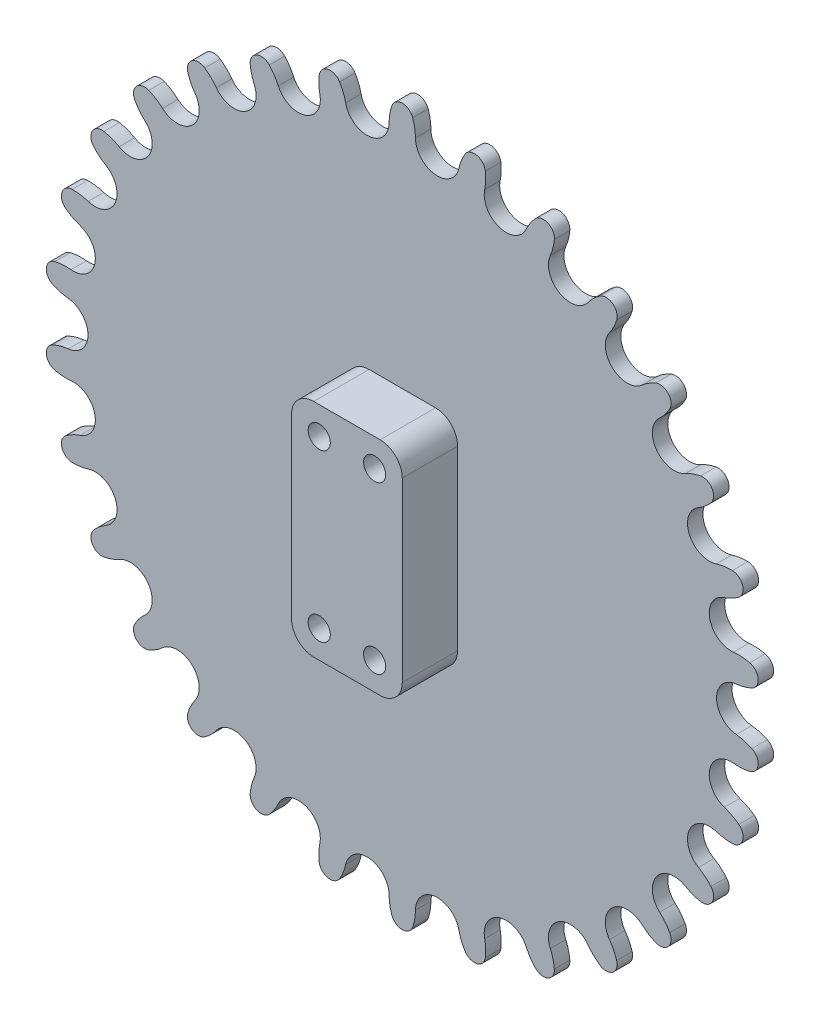
SolidWorks part; units mm, degrees
ref_plane "Front Plane" through (0, 0, 0) normal (0, 0, 1) x (1, 0, 0)
ref_plane "Top Plane" through (0, 0, 0) normal (0, 1, 0) x (1, 0, 0)
ref_plane "Right Plane" through (0, 0, 0) normal (1, 0, 0) x (0, 0, -1)
sketch "Sketch2" plane through (0, 0, 0) normal (0, 0, 1) x (1, 0, 0)
  line L0 (0, 0) -> (-12.7, 0) construction
  line L1 (-6.35, 0) -> (-6.35, -60.4162) construction
  line L2 (-6.35, -60.4162) -> (-12.7, 0) construction
  line L3 (-6.35, -60.4162) -> (0, 0) construction
  line L4 (-6.35, 0) -> (-6.35, 13.4382) construction
  circle A0 centre (0, 0) radius 3.9688 construction
  circle A1 centre (-12.7, 0) radius 3.9688 construction
  arc A2 (-8.7312, 0) -> (-8.2367, 2.8967) centre (0, 0) cw
  arc A3 (-3.9688, 0) -> (-4.4633, 2.8967) centre (-12.7, 0) ccw
  arc A4 (-8.2367, 2.8967) -> (-4.4633, 2.8967) centre (-6.35, 2.2332) cw
  arc A5 (-8.7312, 0) -> (-12.2852, -3.947) centre (-12.7, 0) cw
  arc A6 (-3.9688, 0) -> (-0.4148, -3.947) centre (0, 0) ccw
  arc A7 (8.5405, -1.8153) -> (11.1961, -6.415) centre (12.4225, -2.6405) ccw
  arc A8 (8.5405, -1.8153) -> (8.659, 1.1209) centre (0, 0) ccw
  arc A9 (4.968, 1.9055) -> (8.659, 1.1209) centre (6.6755, 0.8642) cw
  arc A10 (3.882, -0.8251) -> (-0.4148, -3.947) centre (0, 0) cw
  arc A11 (3.882, -0.8251) -> (4.968, 1.9055) centre (12.4225, -2.6405) cw
  arc A12 (20.3989, -6.1918) -> (22.0401, -11.2431) centre (24.0245, -7.806) ccw
  arc A13 (20.3989, -6.1918) -> (21.1253, -3.3443) centre (12.4225, -2.6405) ccw
  arc A14 (17.6781, -1.8095) -> (21.1253, -3.3443) centre (19.1318, -3.1831) cw
  arc A15 (16.0481, -4.2547) -> (11.1961, -6.415) centre (12.4225, -2.6405) cw
  arc A16 (16.0481, -4.2547) -> (17.6781, -1.8095) centre (24.0245, -7.806) cw
  arc A17 (31.0882, -12.9381) -> (31.6434, -18.2203) centre (34.299, -15.2709) ccw
  arc A18 (31.0882, -12.9381) -> (32.3908, -10.3039) centre (24.0245, -7.806) ccw
  arc A19 (29.338, -8.086) -> (32.3908, -10.3039) centre (30.4744, -9.7318) cw
  arc A20 (27.2353, -10.1388) -> (22.0401, -11.2431) centre (24.0245, -7.806) cw
  arc A21 (27.2353, -10.1388) -> (29.338, -8.086) centre (34.299, -15.2709) cw
  arc A22 (40.1414, -21.7595) -> (39.5862, -27.0416) centre (42.797, -24.7088) ccw
  arc A23 (40.1414, -21.7595) -> (41.9632, -19.4537) centre (34.299, -15.2709) ccw
  arc A24 (39.4382, -16.6495) -> (41.9632, -19.4537) centre (40.2076, -18.4956) cw
  arc A25 (36.9546, -18.2203) -> (31.6434, -18.2203) centre (34.299, -15.2709) cw
  arc A26 (36.9546, -18.2203) -> (39.4382, -16.6495) centre (42.797, -24.7088) cw
  arc A27 (47.1626, -32.2703) -> (45.5213, -37.3216) centre (49.147, -35.7074) ccw
  arc A28 (47.1626, -32.2703) -> (49.424, -30.3937) centre (42.797, -24.7088) ccw
  arc A29 (47.5373, -27.1258) -> (49.424, -30.3937) centre (47.906, -29.0915) cw
  arc A30 (44.7814, -28.1459) -> (39.5862, -27.0416) centre (42.797, -24.7088) cw
  arc A31 (44.7814, -28.1459) -> (47.5373, -27.1258) centre (49.147, -35.7074) cw
  arc A32 (51.8451, -44.0113) -> (49.1895, -48.6109) centre (53.0715, -47.7858) ccw
  arc A33 (51.8451, -44.0113) -> (54.4472, -42.6458) centre (49.147, -35.7074) ccw
  arc A34 (53.2812, -39.0571) -> (54.4472, -42.6458) centre (53.2331, -41.0565) cw
  arc A35 (50.3734, -39.4819) -> (45.5213, -37.3216) centre (49.147, -35.7074) cw
  arc A36 (50.3734, -39.4819) -> (53.2812, -39.0571) centre (53.0715, -47.7858) cw
  arc A37 (53.9842, -56.4692) -> (50.4303, -60.4162) centre (54.399, -60.4162) ccw
  arc A38 (53.9842, -56.4692) -> (56.8133, -55.6746) centre (53.0715, -47.7858) ccw
  arc A39 (56.4189, -51.9218) -> (56.8133, -55.6746) centre (55.9562, -53.8676) cw
  arc A40 (53.4863, -51.7328) -> (49.1895, -48.6109) centre (53.0715, -47.7858) cw
  arc A41 (53.4863, -51.7328) -> (56.4189, -51.9218) centre (54.399, -60.4162) cw
  arc A43 (53.4863, -69.0996) -> (49.1895, -72.2215) centre (53.0715, -73.0466) ccw
  arc A44 (53.4863, -69.0996) -> (56.4189, -68.9106) centre (54.399, -60.4162) ccw
  arc A45 (56.8133, -65.1578) -> (56.4189, -68.9106) centre (55.9562, -66.9649) cw
  arc A46 (53.9842, -64.3632) -> (50.4303, -60.4162) centre (54.399, -60.4162) cw
  arc A47 (53.9842, -64.3632) -> (56.8133, -65.1578) centre (53.0715, -73.0466) cw
  arc A48 (50.3734, -81.3506) -> (45.5213, -83.5108) centre (49.147, -85.1251) ccw
  arc A49 (50.3734, -81.3506) -> (53.2812, -81.7754) centre (53.0715, -73.0466) ccw
  arc A50 (54.4472, -78.1866) -> (53.2812, -81.7754) centre (53.2331, -79.776) cw
  arc A51 (51.8451, -76.8211) -> (49.1895, -72.2215) centre (53.0715, -73.0466) cw
  arc A52 (51.8451, -76.8211) -> (54.4472, -78.1866) centre (49.147, -85.1251) cw
  arc A53 (44.7814, -92.6865) -> (39.5862, -93.7908) centre (42.797, -96.1236) ccw
  arc A54 (44.7814, -92.6865) -> (47.5373, -93.7066) centre (49.147, -85.1251) ccw
  arc A55 (49.424, -90.4387) -> (47.5373, -93.7066) centre (47.906, -91.7409) cw
  arc A56 (47.1626, -88.5621) -> (45.5213, -83.5108) centre (49.147, -85.1251) cw
  arc A57 (47.1626, -88.5621) -> (49.424, -90.4387) centre (42.797, -96.1236) cw
  arc A58 (36.9546, -102.6122) -> (31.6434, -102.6122) centre (34.299, -105.5615) ccw
  arc A59 (36.9546, -102.6122) -> (39.4382, -104.183) centre (42.797, -96.1236) ccw
  arc A60 (41.9632, -101.3787) -> (39.4382, -104.183) centre (40.2076, -102.3369) cw
  arc A61 (40.1414, -99.0729) -> (39.5862, -93.7908) centre (42.797, -96.1236) cw
  arc A62 (40.1414, -99.0729) -> (41.9632, -101.3787) centre (34.299, -105.5615) cw
  arc A63 (27.2353, -110.6936) -> (22.0401, -109.5894) centre (24.0245, -113.0264) ccw
  arc A64 (27.2353, -110.6936) -> (29.338, -112.7465) centre (34.299, -105.5615) ccw
  arc A65 (32.3908, -110.5285) -> (29.338, -112.7465) centre (30.4744, -111.1007) cw
  arc A66 (31.0882, -107.8943) -> (31.6434, -102.6122) centre (34.299, -105.5615) cw
  arc A67 (31.0882, -107.8943) -> (32.3908, -110.5285) centre (24.0245, -113.0264) cw
  arc A68 (16.0481, -116.5777) -> (11.1961, -114.4174) centre (12.4225, -118.192) ccw
  arc A69 (16.0481, -116.5777) -> (17.6781, -119.0229) centre (24.0245, -113.0264) ccw
  arc A70 (21.1253, -117.4881) -> (17.6781, -119.0229) centre (19.1318, -117.6493) cw
  arc A71 (20.3989, -114.6406) -> (22.0401, -109.5894) centre (24.0245, -113.0264) cw
  arc A72 (20.3989, -114.6406) -> (21.1253, -117.4881) centre (12.4225, -118.192) cw
  arc A73 (3.882, -120.0073) -> (-0.4148, -116.8854) centre (0, -120.8324) ccw
  arc A74 (3.882, -120.0073) -> (4.968, -122.7379) centre (12.4225, -118.192) ccw
  arc A75 (8.659, -121.9534) -> (4.968, -122.7379) centre (6.6755, -121.6966) cw
  arc A76 (8.5405, -119.0171) -> (11.1961, -114.4174) centre (12.4225, -118.192) cw
  arc A77 (8.5405, -119.0171) -> (8.659, -121.9534) centre (0, -120.8324) cw
  arc A78 (-8.7312, -120.8324) -> (-12.2852, -116.8854) centre (-12.7, -120.8324) ccw
  arc A79 (-8.7312, -120.8324) -> (-8.2367, -123.7292) centre (0, -120.8324) ccw
  arc A80 (-4.4633, -123.7292) -> (-8.2367, -123.7292) centre (-6.35, -123.0656) cw
  arc A81 (-3.9687, -120.8324) -> (-0.4148, -116.8854) centre (0, -120.8324) cw
  arc A82 (-3.9687, -120.8324) -> (-4.4633, -123.7292) centre (-12.7, -120.8324) cw
  arc A83 (-21.2405, -119.0171) -> (-23.8961, -114.4174) centre (-25.1225, -118.192) ccw
  arc A84 (-21.2405, -119.0171) -> (-21.359, -121.9534) centre (-12.7, -120.8324) ccw
  arc A85 (-17.668, -122.7379) -> (-21.359, -121.9534) centre (-19.3755, -121.6966) cw
  arc A86 (-16.582, -120.0073) -> (-12.2852, -116.8854) centre (-12.7, -120.8324) cw
  arc A87 (-16.582, -120.0073) -> (-17.668, -122.7379) centre (-25.1225, -118.192) cw
  arc A88 (-33.0989, -114.6406) -> (-34.7401, -109.5894) centre (-36.7245, -113.0264) ccw
  arc A89 (-33.0989, -114.6406) -> (-33.8253, -117.4881) centre (-25.1225, -118.192) ccw
  arc A90 (-30.3781, -119.0229) -> (-33.8253, -117.4881) centre (-31.8318, -117.6493) cw
  arc A91 (-28.7481, -116.5777) -> (-23.8961, -114.4174) centre (-25.1225, -118.192) cw
  arc A92 (-28.7481, -116.5777) -> (-30.3781, -119.0229) centre (-36.7245, -113.0264) cw
  arc A93 (-43.7882, -107.8943) -> (-44.3434, -102.6122) centre (-46.999, -105.5615) ccw
  arc A94 (-43.7882, -107.8943) -> (-45.0908, -110.5285) centre (-36.7245, -113.0264) ccw
  arc A95 (-42.038, -112.7465) -> (-45.0908, -110.5285) centre (-43.1744, -111.1007) cw
  arc A96 (-39.9353, -110.6936) -> (-34.7401, -109.5894) centre (-36.7245, -113.0264) cw
  arc A97 (-39.9353, -110.6936) -> (-42.038, -112.7465) centre (-46.999, -105.5615) cw
  arc A98 (-52.8414, -99.0729) -> (-52.2862, -93.7908) centre (-55.497, -96.1236) ccw
  arc A99 (-52.8414, -99.0729) -> (-54.6632, -101.3787) centre (-46.999, -105.5615) ccw
  arc A100 (-52.1382, -104.183) -> (-54.6632, -101.3787) centre (-52.9076, -102.3369) cw
  arc A101 (-49.6546, -102.6122) -> (-44.3434, -102.6122) centre (-46.999, -105.5615) cw
  arc A102 (-49.6546, -102.6122) -> (-52.1382, -104.183) centre (-55.497, -96.1236) cw
  arc A103 (-59.8626, -88.5621) -> (-58.2213, -83.5108) centre (-61.847, -85.1251) ccw
  arc A104 (-59.8626, -88.5621) -> (-62.124, -90.4387) centre (-55.497, -96.1236) ccw
  arc A105 (-60.2373, -93.7066) -> (-62.124, -90.4387) centre (-60.606, -91.7409) cw
  arc A106 (-57.4814, -92.6865) -> (-52.2862, -93.7908) centre (-55.497, -96.1236) cw
  arc A107 (-57.4814, -92.6865) -> (-60.2373, -93.7066) centre (-61.847, -85.1251) cw
  arc A108 (-64.5451, -76.8211) -> (-61.8895, -72.2215) centre (-65.7715, -73.0466) ccw
  arc A109 (-64.5451, -76.8211) -> (-67.1472, -78.1866) centre (-61.847, -85.1251) ccw
  arc A110 (-65.9812, -81.7754) -> (-67.1472, -78.1866) centre (-65.9331, -79.776) cw
  arc A111 (-63.0734, -81.3506) -> (-58.2213, -83.5108) centre (-61.847, -85.1251) cw
  arc A112 (-63.0734, -81.3506) -> (-65.9812, -81.7754) centre (-65.7715, -73.0466) cw
  arc A113 (-66.6842, -64.3632) -> (-63.1303, -60.4162) centre (-67.099, -60.4162) ccw
  arc A114 (-66.6842, -64.3632) -> (-69.5133, -65.1578) centre (-65.7715, -73.0466) ccw
  arc A115 (-69.1189, -68.9106) -> (-69.5133, -65.1578) centre (-68.6562, -66.9649) cw
  arc A116 (-66.1863, -69.0996) -> (-61.8895, -72.2215) centre (-65.7715, -73.0466) cw
  arc A117 (-66.1863, -69.0996) -> (-69.1189, -68.9106) centre (-67.099, -60.4162) cw
  arc A118 (-66.1863, -51.7328) -> (-61.8895, -48.6109) centre (-65.7715, -47.7858) ccw
  arc A119 (-66.1863, -51.7328) -> (-69.1189, -51.9218) centre (-67.099, -60.4162) ccw
  arc A120 (-69.5133, -55.6746) -> (-69.1189, -51.9218) centre (-68.6562, -53.8676) cw
  arc A121 (-66.6842, -56.4692) -> (-63.1303, -60.4162) centre (-67.099, -60.4162) cw
  arc A122 (-66.6842, -56.4692) -> (-69.5133, -55.6746) centre (-65.7715, -47.7858) cw
  arc A123 (-63.0734, -39.4819) -> (-58.2213, -37.3216) centre (-61.847, -35.7074) ccw
  arc A124 (-63.0734, -39.4819) -> (-65.9812, -39.0571) centre (-65.7715, -47.7858) ccw
  arc A125 (-67.1472, -42.6458) -> (-65.9812, -39.0571) centre (-65.9331, -41.0565) cw
  arc A126 (-64.5451, -44.0113) -> (-61.8895, -48.6109) centre (-65.7715, -47.7858) cw
  arc A127 (-64.5451, -44.0113) -> (-67.1472, -42.6458) centre (-61.847, -35.7074) cw
  arc A128 (-57.4814, -28.1459) -> (-52.2862, -27.0416) centre (-55.497, -24.7088) ccw
  arc A129 (-57.4814, -28.1459) -> (-60.2373, -27.1258) centre (-61.847, -35.7074) ccw
  arc A130 (-62.124, -30.3937) -> (-60.2373, -27.1258) centre (-60.606, -29.0915) cw
  arc A131 (-59.8626, -32.2703) -> (-58.2213, -37.3216) centre (-61.847, -35.7074) cw
  arc A132 (-59.8626, -32.2703) -> (-62.124, -30.3937) centre (-55.497, -24.7088) cw
  arc A133 (-49.6546, -18.2203) -> (-44.3434, -18.2203) centre (-46.999, -15.2709) ccw
  arc A134 (-49.6546, -18.2203) -> (-52.1382, -16.6495) centre (-55.497, -24.7088) ccw
  arc A135 (-54.6632, -19.4537) -> (-52.1382, -16.6495) centre (-52.9076, -18.4956) cw
  arc A136 (-52.8414, -21.7595) -> (-52.2862, -27.0416) centre (-55.497, -24.7088) cw
  arc A137 (-52.8414, -21.7595) -> (-54.6632, -19.4537) centre (-46.999, -15.2709) cw
  arc A138 (-39.9353, -10.1388) -> (-34.7401, -11.2431) centre (-36.7245, -7.806) ccw
  arc A139 (-39.9353, -10.1388) -> (-42.038, -8.086) centre (-46.999, -15.2709) ccw
  arc A140 (-45.0908, -10.3039) -> (-42.038, -8.086) centre (-43.1744, -9.7318) cw
  arc A141 (-43.7882, -12.9381) -> (-44.3434, -18.2203) centre (-46.999, -15.2709) cw
  arc A142 (-43.7882, -12.9381) -> (-45.0908, -10.3039) centre (-36.7245, -7.806) cw
  arc A143 (-28.7481, -4.2547) -> (-23.8961, -6.415) centre (-25.1225, -2.6405) ccw
  arc A144 (-28.7481, -4.2547) -> (-30.3781, -1.8095) centre (-36.7245, -7.806) ccw
  arc A145 (-33.8253, -3.3443) -> (-30.3781, -1.8095) centre (-31.8318, -3.1831) cw
  arc A146 (-33.0989, -6.1918) -> (-34.7401, -11.2431) centre (-36.7245, -7.806) cw
  arc A147 (-33.0989, -6.1918) -> (-33.8253, -3.3443) centre (-25.1225, -2.6405) cw
  arc A148 (-16.582, -0.8251) -> (-12.2852, -3.947) centre (-12.7, 0) ccw
  arc A149 (-16.582, -0.8251) -> (-17.668, 1.9055) centre (-25.1225, -2.6405) ccw
  arc A150 (-21.359, 1.1209) -> (-17.668, 1.9055) centre (-19.3755, 0.8642) cw
  arc A151 (-21.2405, -1.8153) -> (-23.8961, -6.415) centre (-25.1225, -2.6405) cw
  arc A152 (-21.2405, -1.8153) -> (-21.359, 1.1209) centre (-12.7, 0) cw
  dimension "D1" = 7.9375
  dimension "D4" = 2
  dimension "D2" = 12.7
  dimension "D3" = 12
extrude "Boss-Extrude1" add sketch "Sketch2" along normal blind 2.794
sketch "Sketch3" plane through (0, 0, 2.794) normal (0, 0, 1) x (1, 0, 0)
  line L0 (-6.35, -60.4162) -> (-6.35, -13.0662) construction
  line L1 (-0.35, -40.4162) -> (-12.35, -40.4162)
  line L2 (-16.35, -44.4162) -> (-16.35, -76.4162)
  line L3 (-6.35, -60.4162) -> (-28.0397, -60.4162) construction
  line L4 (-0.35, -80.4162) -> (-12.35, -80.4162)
  line L5 (3.65, -44.4162) -> (3.65, -76.4162)
  arc A0 (-12.35, -80.4162) -> (-16.35, -76.4162) centre (-12.35, -76.4162) cw
  arc A1 (3.65, -76.4162) -> (-0.35, -80.4162) centre (-0.35, -76.4162) cw
  arc A2 (3.65, -44.4162) -> (-0.35, -40.4162) centre (-0.35, -44.4162) ccw
  arc A3 (-12.35, -40.4162) -> (-16.35, -44.4162) centre (-12.35, -44.4162) ccw
  point P8 (-16.35, -60.4162)
  point P10 (-6.35, -40.4162)
  point P11 (-6.35, -80.4162)
  point P13 (-16.35, -80.4162)
  point P16 (3.65, -80.4162)
  point P19 (3.65, -40.4162)
  point P22 (-16.35, -40.4162)
  dimension "D1" = 10
  dimension "D2" = 20
  dimension "D3" = 4
sketch "Sketch5" plane through (0, 0, 0) normal (0, 0, -1) x (-1, 0, 0)
  circle A0 centre (6.35, -60.4162) radius 4
  dimension "D1" = 8
extrude "Boss-Extrude3" add sketch "Sketch5" along normal blind 32.206
extrude "Boss-Extrude4" add sketch "Sketch3" along normal blind 10
sketch "Sketch6" plane through (0, 0, 12.794) normal (0, 0, 1) x (1, 0, 0)
  line L0 (-6.35, -40.4162) -> (-6.35, -80.4162) construction
  line L1 (-0.35, -40.4162) -> (-12.35, -40.4162) construction
  line L2 (-12.35, -80.4162) -> (-0.35, -80.4162) construction
  line L3 (-6.35, -60.4162) -> (-16.35, -60.4162) construction
  line L4 (-16.35, -44.4162) -> (-16.35, -76.4162) construction
  line L6 (-0.35, -40.4162) -> (-12.35, -40.4162) construction
  circle A0 centre (-11.35, -45.4162) radius 2
  circle A1 centre (-11.35, -75.4162) radius 2
  circle A2 centre (-1.35, -75.4162) radius 2
  circle A3 centre (-1.35, -45.4162) radius 2
  point P21 (-8.658, -20.0923)
  point P22 (0, 0)
  dimension "D1" = 4
  dimension "D2" = 5
  dimension "D3" = 5
extrude "Cut-Extrude1" cut sketch "Sketch6" against normal through all
sketch "Sketch7" plane through (0, 0, 2.794) normal (0, 0, 1) x (1, 0, 0)
  circle A0 centre (-6.35, -60.4162) radius 5
  dimension "D1" = 10
extrude "Boss-Extrude5" add sketch "Sketch7" against normal blind 19
